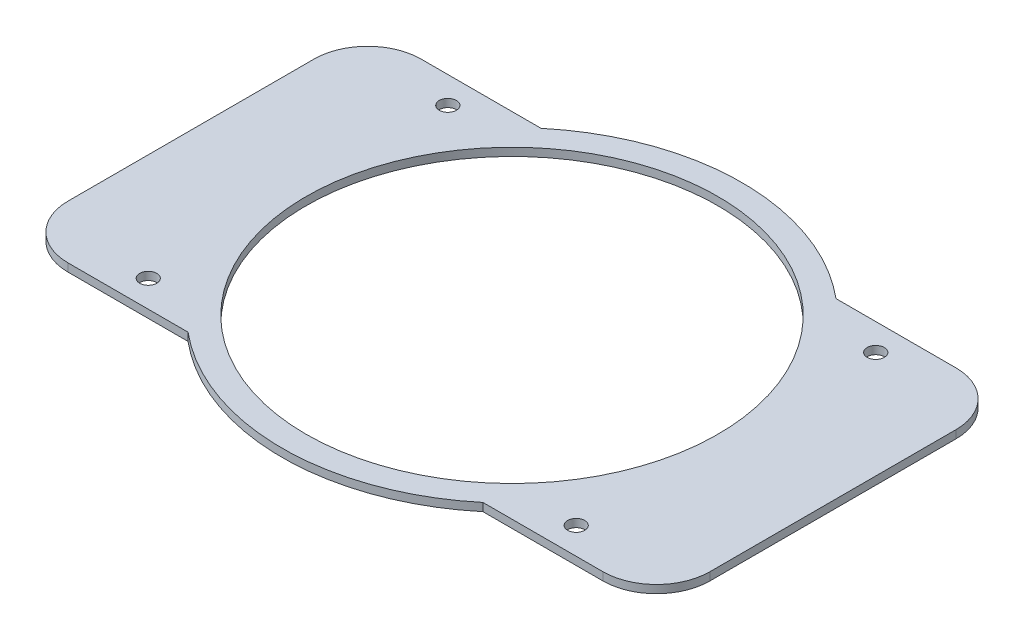
SolidWorks part; units mm, degrees
ref_plane "Front" through (0, 0, 0) normal (0, 0, 1) x (1, 0, 0)
ref_plane "Top" through (0, 0, 0) normal (0, 1, 0) x (1, 0, 0)
ref_plane "Right" through (0, 0, 0) normal (1, 0, 0) x (0, 0, -1)
sketch "Sketch2" plane through (0, 0, 0) normal (0, 1, 0) x (1, 0, 0)
  line L1 (-60, 32) -> (-28.7228, 32)
  line L2 (60, 32) -> (60, -32)
  line L3 (60, -32) -> (28.7228, -32)
  line L5 (-60, 32) -> (-60, -32)
  line L6 (-28.7228, -32) -> (-60, -32)
  line L7 (28.7228, 32) -> (60, 32)
  circle A0 centre (0, 0) radius 38.5
  arc A1 (-28.7228, -32) -> (28.7228, -32) centre (0, 0) ccw
  arc A2 (28.7228, 32) -> (-28.7228, 32) centre (0, 0) ccw
extrude "Boss-Extrude4" add sketch "Sketch2" along normal blind 1.5
sketch "Sketch3" plane through (0, 1.5, 0) normal (0, 1, 0) x (1, 0, 0)
  line L0 (60, 32) -> (60, 33)
  line L1 (60, 33) -> (22.9676, 33)
  line L2 (22.9676, 33) -> (40.7592, 20.4964)
  line L3 (40.7592, 20.4964) -> (60, 20.4964)
  line L4 (60, -32) -> (60, 32) construction
  line L5 (60, 20.4964) -> (60, 32)
  line L7 (60, -20.4964) -> (60, -32)
  line L8 (40.7592, -20.4964) -> (60, -20.4964)
  line L9 (22.9676, -33) -> (40.7592, -20.4964)
  line L10 (60, -33) -> (22.9676, -33)
  line L11 (60, -32) -> (60, -33)
  line L13 (-60, -32) -> (-60, -33)
  line L14 (-60, -33) -> (-22.9676, -33)
  line L15 (-22.9676, -33) -> (-40.7592, -20.4964)
  line L16 (-40.7592, -20.4964) -> (-60, -20.4964)
  line L17 (-60, -20.4964) -> (-60, -32)
  line L18 (-60, 20.4964) -> (-60, 32)
  line L19 (-40.7592, 20.4964) -> (-60, 20.4964)
  line L20 (-22.9676, 33) -> (-40.7592, 20.4964)
  line L21 (-60, 33) -> (-22.9676, 33)
  line L22 (-60, 32) -> (-60, 33)
extrude "Boss-Extrude5" add sketch "Sketch3" against normal up to surface (1.5 mm away) up to face at (0, 0, 0)
sketch "Sketch4" plane through (0, 1.5, 0) normal (0, 1, 0) x (1, 0, 0)
  circle A0 centre (40, 28) radius 1.6
  circle A1 centre (40, -28) radius 1.6
  circle A2 centre (-40, -28) radius 1.6
  circle A3 centre (-40, 28) radius 1.6
extrude "Cut-Extrude1" cut sketch "Sketch4" against normal blind 1.5
fillet "Fillet1" radius 10 4 edges at (60, 0.75, 33) (60, 0.75, -33) (-60, 0.75, -33) (-60, 0.75, 33)
